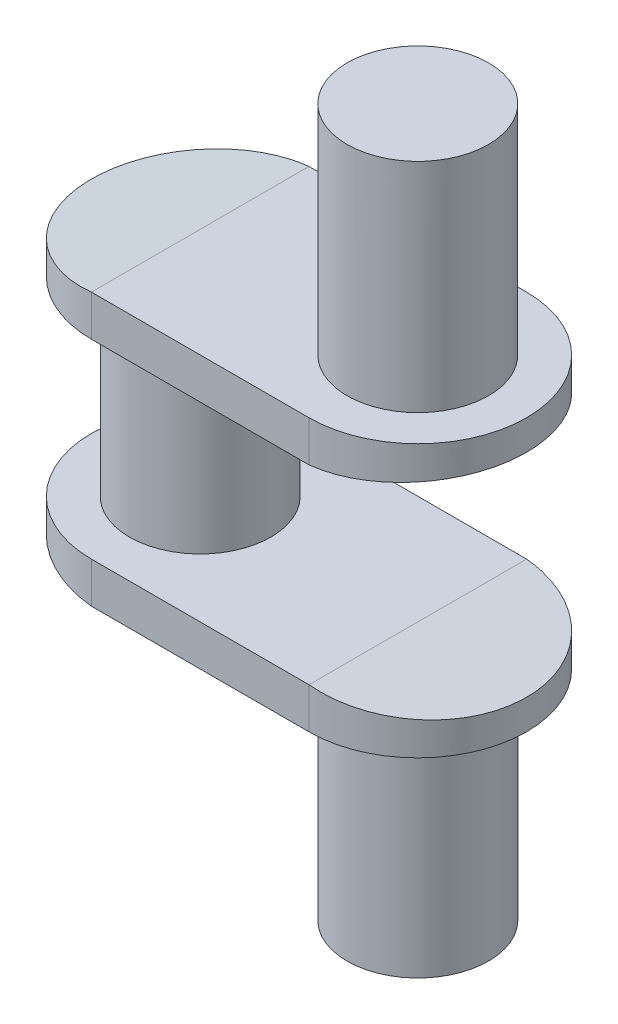
SolidWorks part; units mm, degrees
ref_plane "Front Plane" through (0, 0, 0) normal (0, 0, 1) x (1, 0, 0)
ref_plane "Top Plane" through (0, 0, 0) normal (0, 1, 0) x (1, 0, 0)
ref_plane "Right Plane" through (0, 0, 0) normal (1, 0, 0) x (0, 0, -1)
sketch "Sketch1" plane through (0, 0, 0) normal (0, 1, 0) x (1, 0, 0)
  circle A0 centre (0, 0) radius 26
  dimension "D1" = 52
extrude "Boss-Extrude1" add sketch "Sketch1" along normal mid plane 70
sketch "Sketch3" plane through (0, 35, 0) normal (0, 1, 0) x (1, 0, 0)
  line L0 (0, 40) -> (80, 40)
  line L1 (0, -40) -> (80, -40)
  arc A0 (0, -40) -> (0, 40) centre (0, 0) cw
  arc A1 (80, 40) -> (80, -40) centre (80, 0) cw
  point P7 (0, 0)
  dimension "D2" = 40
  dimension "D1" = 0
  dimension "D3" = 80
  dimension "D4" = 80
extrude "Boss-Extrude2" add sketch "Sketch3" along normal blind 15
mirror "Mirror2" about plane through (0, 0, 0) normal (0, 1, 0) of "Boss-Extrude2"
sketch "Sketch5" plane through (0, 50, 0) normal (0, 1, 0) x (1, 0, 0)
  circle A0 centre (80, 0) radius 26
  dimension "D1" = 52
extrude "Boss-Extrude3" add sketch "Sketch5" along normal blind 80
mirror "Mirror3" about plane through (0, 0, 0) normal (0, 1, 0) of "Boss-Extrude3"
sketch "Sketch6" plane through (0, 0, 0) normal (0, 0, 1) x (1, 0, 0)
  line L0 (0, 0) -> (-141.3532, 0) construction
  line L1 (0, -50) -> (-40, -50)
  line L2 (-40, -50) -> (-40, -46)
  line L3 (-40, -35) -> (-40, -50) construction
  line L4 (-40, -46) -> (0, -50)
  line L5 (80, -35) -> (120, -35)
  line L6 (120, -35) -> (120, -39)
  line L7 (120, -39) -> (80, -35)
  line L8 (120, 39) -> (80, 35)
  line L9 (120, 35) -> (120, 39)
  line L10 (80, 35) -> (120, 35)
  line L11 (-40, 46) -> (0, 50)
  line L12 (-40, 50) -> (-40, 46)
  line L13 (0, 50) -> (-40, 50)
  point P21 (0, 0)
  dimension "D1" = 4
  dimension "D2" = 4
extrude "Cut-Extrude2" cut sketch "Sketch6" against normal through all both and the other way through all contours L4 L1 L2 | L7 L5 L6 | L8 L10 L9 | L11 L13 L12
